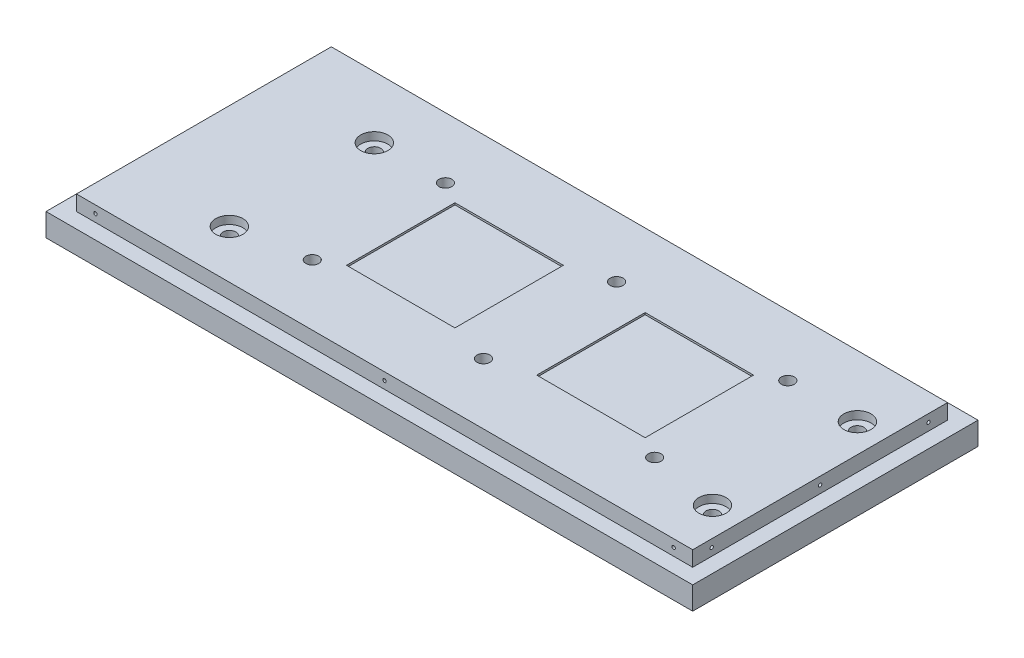
SolidWorks part; units mm, degrees
ref_plane "Front Plane" through (0, 0, 0) normal (0, 0, 1) x (1, 0, 0)
ref_plane "Top Plane" through (0, 0, 0) normal (0, 1, 0) x (1, 0, 0)
ref_plane "Right Plane" through (0, 0, 0) normal (1, 0, 0) x (0, 0, -1)
sketch "Sketch1" plane through (0, 0, 0) normal (0, 1, 0) x (1, 0, 0)
  line L1 (0, 0) -> (340, 0)
  line L2 (0, 0) -> (0, 150)
  line L3 (0, 150) -> (340, 150)
  line L4 (340, 0) -> (340, 150)
  dimension "D1" = 150
  dimension "D2" = 340
extrude "Boss-Extrude1" add sketch "Sketch1" along normal blind 20
hole_wizard "LaserCavityMountingHole_CBORE for 1/4 Socket Head Cap Screw1" positions "Sketch3" profile "Sketch4" counterbore size "1/4" standard "ANSI Inch" end condition through all
sketch "Sketch3" plane through (0, 0, 0) normal (0, -1, 0) x (-1, 0, 0)
  line L8 (-90, 120) -> (-290, 120)
  line L9 (-90, 120) -> (-90, 30)
  line L10 (-90, 30) -> (-290, 30)
  line L11 (-290, 120) -> (-290, 30)
  line L14 (-190, 120) -> (-190, 30) construction
  line L15 (0, 150) -> (0, 0) construction
  line L16 (-290, 75) -> (-90, 75) construction
  line L17 (-90, 75) -> (0, 75) construction
  line L18 (0, 150) -> (0, 0) construction
  line L21 (0, 75) -> (-340, 75) construction
  line L22 (-340, 0) -> (-340, 150) construction
  line L23 (-340, 0) -> (-340, 150) construction
  point P0 (-100, 40)
  point P2 (-190, 40)
  point P4 (-280, 40)
  point P6 (-280, 110)
  point P8 (-190, 110)
  point P10 (-100, 110)
  point P111 (-340, 75)
  dimension "D2" = 200
  dimension "D3" = 90
  dimension "D4" = 0
  dimension "D5" = 90
  dimension "D6" = 10
  dimension "D7" = 10
  dimension "D8" = 10
  dimension "D9" = 10
  dimension "D10" = 10
  dimension "D11" = 0
  dimension "D12" = 0
  dimension "D13" = 10
  dimension "D14" = 10
  dimension "D15" = 10
  dimension "D16" = 10
  dimension "D17" = 10
  dimension "D18" = 10
sketch "Sketch4" plane through (100, 0, -40) normal (1, 0, 0) x (0, 0, -1)
  line L0 (0, 0) -> (0, 20)
  line L1 (0, 20) -> (3.3782, 20)
  line L3 (3.3782, 20) -> (3.3782, 6.35)
  line L4 (3.3782, 6.35) -> (5.5562, 6.35)
  line L5 (5.5562, 6.35) -> (5.5562, 0)
  line L7 (5.5562, 0) -> (0, 0)
  line L11 (0, -6.35) -> (0, 107.95) construction
  dimension "Thru Hole Dia." = 6.7564
  dimension "Thru Hole Depth" = 20
  dimension "C'Bore Dia." = 11.1125
  dimension "C'Bore Depth" = 6.35
sketch "Sketch5" plane through (0, 20, 0) normal (0, 1, 0) x (1, 0, 0)
  line L0 (90, 30) -> (290, 30) construction
  line L1 (111.5, 103.5) -> (168.5, 103.5)
  line L2 (111.5, 103.5) -> (111.5, 46.5)
  line L3 (111.5, 46.5) -> (168.5, 46.5)
  line L4 (168.5, 103.5) -> (168.5, 46.5)
  line L5 (190, 120) -> (190, 30) construction
  line L11 (211.5, 103.5) -> (268.5, 103.5)
  line L12 (211.5, 103.5) -> (211.5, 46.5)
  line L13 (211.5, 46.5) -> (268.5, 46.5)
  line L14 (268.5, 103.5) -> (268.5, 46.5)
  point P4 (168.5, 75)
  point P7 (211.5, 75)
  point P8 (140, 46.5)
  point P11 (240, 46.5)
  dimension "D1" = 57
  dimension "D2" = 57
  dimension "D3" = 45
  dimension "D4" = 45
  dimension "D5" = 57
  dimension "D6" = 57
  dimension "D7" = 50
  dimension "D8" = 50
extrude "TEC_groove" cut sketch "Sketch5" against normal blind 1
sketch "Sketch6" plane through (0, 0, 0) normal (0, 0, 1) x (1, 0, 0)
  line L0 (340, 20) -> (340, 0) construction
  line L1 (0, 20) -> (340, 20)
  line L2 (0, 20) -> (0, 12)
  line L3 (0, 12) -> (340, 12)
  line L4 (340, 20) -> (340, 12)
  dimension "D1" = 8
extrude "Wall1" cut sketch "Sketch6" against normal blind 8
sketch "Sketch7" plane through (340, 0, 0) normal (1, 0, 0) x (0, 0, -1)
  line L0 (8, 12) -> (8, 20) construction
  line L1 (150, 20) -> (8, 20)
  line L2 (150, 20) -> (150, 12)
  line L3 (150, 12) -> (8, 12)
  line L4 (8, 20) -> (8, 12)
  dimension "D1" = 8
extrude "Wall2" cut sketch "Sketch7" against normal blind 8
sketch "Sketch9" plane through (0, 0, -150) normal (0, 0, -1) x (-1, 0, 0)
  line L0 (-332, 12) -> (-332, 20) construction
  line L1 (0, 20) -> (-332, 20)
  line L2 (0, 20) -> (0, 12)
  line L3 (0, 12) -> (-332, 12)
  line L4 (-332, 20) -> (-332, 12)
  dimension "D1" = 8
extrude "Wall3" cut sketch "Sketch9" against normal blind 8
sketch "Sketch10" plane through (0, 0, 0) normal (-1, 0, 0) x (0, 0, 1)
  line L1 (-142, 20) -> (-8, 20)
  line L2 (-142, 20) -> (-142, 12)
  line L3 (-142, 12) -> (-8, 12)
  line L4 (-8, 20) -> (-8, 12)
extrude "Wall4" cut sketch "Sketch10" against normal blind 8
hole_wizard "#2-56 Tapped Hole1" positions "Sketch13" profile "Sketch12" tap size "#2-56" standard "ANSI Inch"
sketch "Sketch13" plane through (0, 0, -8) normal (0, 0, 1) x (1, 0, 0)
  line L0 (8, 12) -> (8, 20) construction
  line L1 (8, 16) -> (332, 16) construction
  line L2 (332, 20) -> (332, 12) construction
  point P0 (18, 16)
  point P1 (322, 16)
  point P10 (170, 16)
  dimension "D1" = 10
  dimension "D2" = 0
  dimension "D3" = 10
  dimension "D4" = 0
sketch "Sketch12" plane through (18, 16, -8) normal (1, 0, 0) x (0, -1, 0)
  line L0 (0, 0) -> (0, 15.5342)
  line L1 (0, 15.5342) -> (0.889, 15)
  line L2 (0.889, 15) -> (0.889, 0)
  line L5 (0.889, 0) -> (0, 0)
  line L10 (0, 15.5342) -> (-0.889, 15) construction
  line L11 (0, -6.35) -> (0, 107.95) construction
  dimension "Tap Drill Dia." = 1.778
  dimension "Tap Drill Depth" = 15
  dimension "Drill Angle" = 118
cosmetic thread "Hole Thread1" parameters "D1"=12, "D2"=2.1844
cosmetic thread "Hole Thread2" parameters "D1"=12, "D2"=2.1844
cosmetic thread "Hole Thread13" parameters "D1"=12, "D2"=2.1844
hole_wizard "#2-56 Tapped Hole2" positions "3DSketch2" profile "Sketch15" tap size "#2-56" standard "ANSI Inch"
sketch3d "3DSketch2"
  line L0 (8, 20, -142) -> (8, 12, -142) construction
  line L1 (8, 16, -142) -> (8, 16, -8) construction
  line L2 (8, 12, -8) -> (8, 20, -8) construction
  line L3 (8, 20, -75) -> (8, 12, -75) construction
  line L4 (8, 20, -8) -> (8, 20, -142) construction
  line L5 (8, 12, -142) -> (8, 12, -8) construction
  point P0 (8, 16, -132)
  point P2 (8, 16, -18)
  point P11 (8, 16, -75)
  point P14 (8, 16, -75)
  point P16 (8, 16, -75)
  point P19 (8, 16, -75)
  point P21 (8, 16, -75)
  point P23 (8, 16, -91.6124)
  point P25 (8, 16, -75)
  point P28 (8, 16, -75)
  point P30 (8, 16, -75)
  point P46 (8, 16, -75)
  point P48 (8, 16, -75)
  point P50 (8, 16, -121.0214)
  point P52 (8, 16, -75)
  dimension "D1" = 10
  dimension "D2" = 10
  dimension "D3" = 0
  dimension "D4" = 0
  dimension "D5" = 0
  dimension "D6" = 0
sketch "Sketch15" plane through (8, 16, -132) normal (0, 1, 0) x (0, 0, 1)
  line L0 (0, 0) -> (0, 15.5342)
  line L1 (0, 15.5342) -> (0.889, 15)
  line L2 (0.889, 15) -> (0.889, 0)
  line L5 (0.889, 0) -> (0, 0)
  line L10 (0, 15.5342) -> (-0.889, 15) construction
  line L11 (0, -6.35) -> (0, 107.95) construction
  dimension "Tap Drill Dia." = 1.778
  dimension "Tap Drill Depth" = 15
  dimension "Drill Angle" = 118
cosmetic thread "Hole Thread3" parameters "D1"=12, "D2"=2.1844
cosmetic thread "Hole Thread4" parameters "D1"=12, "D2"=2.1844
cosmetic thread "Hole Thread40" parameters "D1"=12, "D2"=2.1844
sketch "Sketch16" plane through (8, 0, 0) normal (-1, 0, 0) x (0, 0, 1)
  line L0 (-142, 16) -> (-8, 16) construction
  line L1 (-142, 20) -> (-142, 12) construction
  line L2 (-8, 12) -> (-8, 20) construction
sketch "Sketch17" plane through (332, 0, 0) normal (1, 0, 0) x (0, 0, -1)
  line L0 (8, 16) -> (142, 16) construction
  line L1 (8, 20) -> (8, 12) construction
  line L2 (142, 20) -> (142, 12) construction
sketch "Sketch18" plane through (332, 0, 0) normal (1, 0, 0) x (0, 0, -1)
  line L0 (8, 16) -> (142, 16) construction
hole_wizard "#2-56 Tapped Hole3" positions "Sketch19" profile "Sketch20" tap size "#2-56" standard "ANSI Inch"
sketch "Sketch19" plane through (0, 0, -142) normal (0, 0, -1) x (-1, 0, 0)
  line L0 (-332, 16) -> (-8, 16) construction
  line L1 (-332, 20) -> (-332, 12) construction
  line L2 (-8, 20) -> (-8, 12) construction
  point P0 (-322, 16)
  point P2 (-18, 16)
  point P11 (-170, 16)
  dimension "D1" = 0
  dimension "D2" = 10
  dimension "D3" = 0
  dimension "D4" = 10
sketch "Sketch20" plane through (322, 16, -142) normal (1, 0, 0) x (0, 1, 0)
  line L0 (0, 0) -> (0, 15.5342)
  line L1 (0, 15.5342) -> (0.889, 15)
  line L2 (0.889, 15) -> (0.889, 0)
  line L5 (0.889, 0) -> (0, 0)
  line L10 (0, 15.5342) -> (-0.889, 15) construction
  line L11 (0, -6.35) -> (0, 107.95) construction
  dimension "Tap Drill Dia." = 1.778
  dimension "Tap Drill Depth" = 15
  dimension "Drill Angle" = 118
cosmetic thread "Hole Thread5" parameters "D1"=12, "D2"=2.1844
cosmetic thread "Hole Thread6" parameters "D1"=12, "D2"=2.1844
cosmetic thread "Hole Thread22" parameters "D1"=12, "D2"=2.1844
hole_wizard "#2-56 Tapped Hole4" positions "Sketch23" profile "Sketch24" tap size "#2-56" standard "ANSI Inch"
sketch "Sketch23" plane through (332, 0, 0) normal (1, 0, 0) x (0, 0, -1)
  line L0 (142, 16) -> (8, 16) construction
  line L1 (8, 20) -> (8, 12) construction
  line L2 (142, 20) -> (142, 12) construction
  point P0 (18, 16)
  point P4 (132, 16)
  point P11 (75, 16)
  dimension "D1" = 10
  dimension "D2" = 10
sketch "Sketch24" plane through (332, 16, -18) normal (0, 1, 0) x (0, 0, -1)
  line L0 (0, 0) -> (0, 15.5342)
  line L1 (0, 15.5342) -> (0.889, 15)
  line L2 (0.889, 15) -> (0.889, 0)
  line L5 (0.889, 0) -> (0, 0)
  line L10 (0, 15.5342) -> (-0.889, 15) construction
  line L11 (0, -6.35) -> (0, 107.95) construction
  dimension "Tap Drill Dia." = 1.778
  dimension "Tap Drill Depth" = 15
  dimension "Drill Angle" = 118
cosmetic thread "Hole Thread11" parameters "D1"=12, "D2"=2.1844
cosmetic thread "Hole Thread12" parameters "D1"=12, "D2"=2.1844
cosmetic thread "Hole Thread23" parameters "D1"=12, "D2"=2.1844
hole_wizard "OpticalTableMountingHoles_CBORE for 1/4 Binding Head Machine Screw1" positions "Sketch25" profile "Sketch26" counterbore size "1/4" standard "ANSI Inch"
sketch "Sketch25" plane through (0, 20, 0) normal (0, 1, 0) x (1, 0, 0)
  line L0 (332, 8) -> (332, 142) construction
  line L1 (332, 8) -> (8, 8) construction
  point P0 (63, 109.6)
  point P2 (317, 109.6)
  point P4 (317, 33.4)
  point P6 (63, 33.4)
  dimension "D1" = 15
  dimension "D2" = 25.4
  dimension "D3" = 76.2
  dimension "D4" = 0
  dimension "D5" = 254
  dimension "D6" = 0
  dimension "D7" = 254
  dimension "D8" = 76.2
sketch "Sketch26" plane through (63, 20, -109.6) normal (1, 0, 0) x (0, 0, 1)
  line L0 (0, 0) -> (0, 22.0298)
  line L1 (0, 22.0298) -> (3.3782, 20)
  line L2 (3.3782, 20) -> (3.3782, 4.191)
  line L3 (3.3782, 4.191) -> (7.1437, 4.191)
  line L4 (7.1437, 4.191) -> (7.1437, 0)
  line L5 (7.1437, 0) -> (0, 0)
  line L10 (0, 22.0298) -> (-3.3782, 20) construction
  line L11 (0, -6.35) -> (0, 107.95) construction
  dimension "Hole Dia." = 6.7564
  dimension "Hole Depth" = 20
  dimension "C'Bore Dia." = 14.2875
  dimension "C'Bore Depth" = 4.191
  dimension "Drill Angle" = 118
